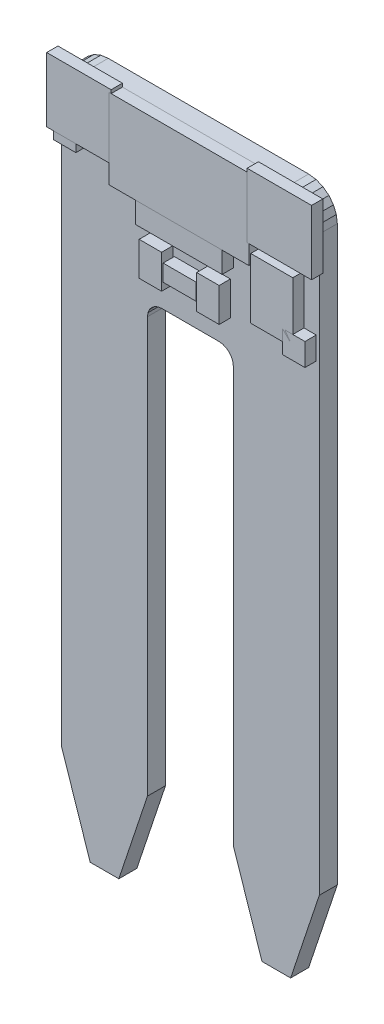
SolidWorks part; units mm, degrees
ref_plane "Front Plane" through (0, 0, 0) normal (0, 0, 1) x (1, 0, 0)
ref_plane "Top Plane" through (0, 0, 0) normal (0, 1, 0) x (1, 0, 0)
ref_plane "Right Plane" through (0, 0, 0) normal (1, 0, 0) x (0, 0, -1)
sketch "Sketch1" plane through (0, 0, 0) normal (0, 0, 1) x (1, 0, 0)
  line L0 (2.54, 60.96) -> (1.8826, 60.8735)
  line L1 (1.8826, 60.8735) -> (1.27, 60.6197)
  line L2 (1.27, 60.6197) -> (0.7439, 60.2161)
  line L3 (0.7439, 60.2161) -> (0.3403, 59.69)
  line L4 (0.3403, 59.69) -> (0.0865, 59.0774)
  line L5 (0.0865, 59.0774) -> (0, 58.42)
  line L6 (0, 58.42) -> (0, 7.62)
  line L7 (0, 7.62) -> (2.54, 0)
  line L8 (2.54, 0) -> (5.08, 0)
  line L9 (5.08, 0) -> (7.62, 7.62)
  line L10 (7.62, 7.62) -> (7.62, 44.45)
  line L11 (7.62, 44.45) -> (7.6633, 44.7787)
  line L12 (7.6633, 44.7787) -> (7.7901, 45.085)
  line L13 (7.7901, 45.085) -> (7.992, 45.348)
  line L14 (7.992, 45.348) -> (8.255, 45.5499)
  line L15 (8.255, 45.5499) -> (8.5613, 45.6767)
  line L16 (8.5613, 45.6767) -> (8.89, 45.72)
  line L17 (8.89, 45.72) -> (13.97, 45.72)
  line L18 (13.97, 45.72) -> (14.2987, 45.6767)
  line L19 (14.2987, 45.6767) -> (14.605, 45.5499)
  line L20 (14.605, 45.5499) -> (14.868, 45.348)
  line L21 (14.868, 45.348) -> (15.0699, 45.085)
  line L22 (15.0699, 45.085) -> (15.1967, 44.7787)
  line L23 (15.1967, 44.7787) -> (15.24, 44.45)
  line L24 (15.24, 44.45) -> (15.24, 7.62)
  line L25 (15.24, 7.62) -> (17.78, 0)
  line L26 (17.78, 0) -> (20.32, 0)
  line L27 (20.32, 0) -> (22.86, 7.62)
  line L28 (22.86, 7.62) -> (22.86, 58.42)
  line L29 (22.86, 58.42) -> (22.7735, 59.0774)
  line L30 (22.7735, 59.0774) -> (22.5197, 59.69)
  line L31 (22.5197, 59.69) -> (22.1161, 60.2161)
  line L32 (22.1161, 60.2161) -> (21.59, 60.6197)
  line L33 (21.59, 60.6197) -> (20.9774, 60.8735)
  line L34 (20.9774, 60.8735) -> (20.32, 60.96)
  line L35 (20.32, 60.96) -> (2.54, 60.96)
extrude "BOARD" add sketch "Sketch1" along normal blind 1.6 separate body
ref_plane "Plane1" through (0, 0, 1.6) normal (0, 0, 1) x (1, 0, 0)
sketch "Sketch2" plane through (0, 0, 1.6) normal (0, 0, 1) x (1, 0, 0)
  line L0 (2.27, 54.88) -> (0.27, 54.88)
  line L1 (0.27, 54.88) -> (0.27, 56.88)
  line L2 (0.27, 56.88) -> (2.27, 56.88)
  line L3 (2.27, 56.88) -> (2.27, 54.88)
extrude "FIDUCIAL-1X2-1" add sketch "Sketch2" along normal blind 1 separate body
sketch "Sketch3" plane through (0, 0, 1.6) normal (0, 0, 1) x (1, 0, 0)
  line L0 (22.59, 48.53) -> (20.59, 48.53)
  line L1 (20.59, 48.53) -> (20.59, 50.53)
  line L2 (20.59, 50.53) -> (22.59, 50.53)
  line L3 (22.59, 50.53) -> (22.59, 48.53)
extrude "FIDUCIAL-1X2-2" add sketch "Sketch3" along normal blind 1 separate body
sketch "Sketch5" plane through (0, 0, 1.6) normal (0, 0, 1) x (1, 0, 0)
  line L0 (7.5565, 57.7215) -> (15.24, 57.7215)
  line L1 (15.24, 57.7215) -> (15.24, 52.0065)
  line L2 (15.24, 52.0065) -> (7.5565, 52.0065)
  line L3 (7.5565, 52.0065) -> (7.5565, 57.7215)
extrude "MOLEX-1X3-1" add sketch "Sketch5" along normal blind 1 separate body
sketch "Sketch6" plane through (0, 0, 1.6) normal (0, 0, 1) x (1, 0, 0)
  line L0 (17.6098, 53.877) -> (5.2098, 53.877)
  line L1 (5.2098, 53.877) -> (5.2098, 60.9786)
  line L2 (5.2098, 60.9786) -> (17.6098, 60.9786)
  line L3 (17.6098, 60.9786) -> (17.6098, 53.877)
extrude "SCREWTERMINAL-3_5MM-3_LOCK_007S-1" add sketch "Sketch6" along normal blind 1 separate body
sketch "Sketch7" plane through (0, 0, 0) normal (0, 0, 1) x (1, 0, 0)
  line L0 (17.78, 53.45) -> (6.45, 53.45)
  line L1 (6.45, 53.45) -> (6.45, 48.26)
  line L2 (6.45, 48.26) -> (17.78, 48.26)
  line L3 (17.78, 48.26) -> (17.78, 53.45)
extrude "SFE_LOGO_NAME_FLAME__1-1" add sketch "Sketch7" against normal blind 1 separate body
sketch "Sketch8" plane through (0, 0, 0) normal (0, 0, 1) x (1, 0, 0)
  line L0 (21.8088, 56.0988) -> (18.8312, 56.0988)
  line L1 (18.8312, 56.0988) -> (18.8312, 53.428)
  line L2 (18.8312, 53.428) -> (21.8088, 53.428)
  line L3 (21.8088, 53.428) -> (21.8088, 56.0988)
extrude "OSHW-LOGO-S-1" add sketch "Sketch8" against normal blind 1 separate body
sketch "Sketch9" plane through (0, 0, 1.6) normal (0, 0, 1) x (1, 0, 0)
  line L0 (10.0076, 50.2666) -> (12.9286, 50.2666)
  line L1 (12.9286, 50.2666) -> (12.9286, 48.7934)
  line L2 (12.9286, 48.7934) -> (10.0076, 48.7934)
  line L3 (10.0076, 48.7934) -> (10.0076, 50.2666)
extrude "SOT23-3-1" add sketch "Sketch9" along normal blind 1 separate body
sketch "Sketch10" plane through (0, 0, 1.6) normal (0, 0, 1) x (1, 0, 0)
  line L0 (14.9784, 51.0284) -> (14.9784, 48.0316)
  line L1 (14.9784, 48.0316) -> (12.987, 48.0316)
  line L2 (12.987, 48.0316) -> (12.987, 51.0284)
  line L3 (12.987, 51.0284) -> (14.9784, 51.0284)
extrude "0603-RES-1" add sketch "Sketch10" along normal blind 1 separate body
sketch "Sketch11" plane through (0, 0, 1.6) normal (0, 0, 1) x (1, 0, 0)
  line L0 (7.8816, 48.0316) -> (7.8816, 51.0284)
  line L1 (7.8816, 51.0284) -> (9.873, 51.0284)
  line L2 (9.873, 51.0284) -> (9.873, 48.0316)
  line L3 (9.873, 48.0316) -> (7.8816, 48.0316)
extrude "0603-RES-2" add sketch "Sketch11" along normal blind 1 separate body
sketch "Sketch12" plane through (0, 0, 1.6) normal (0, 0, 1) x (1, 0, 0)
  line L0 (-0.3175, 61.2775) -> (5.3975, 61.2775)
  line L1 (5.3975, 61.2775) -> (5.3975, 55.5625)
  line L2 (5.3975, 55.5625) -> (-0.3175, 55.5625)
  line L3 (-0.3175, 55.5625) -> (-0.3175, 61.2775)
extrude "STAND-OFF-1" add sketch "Sketch12" along normal blind 1 separate body
sketch "Sketch13" plane through (0, 0, 1.6) normal (0, 0, 1) x (1, 0, 0)
  line L0 (17.4625, 61.2775) -> (23.1775, 61.2775)
  line L1 (23.1775, 61.2775) -> (23.1775, 55.5625)
  line L2 (23.1775, 55.5625) -> (17.4625, 55.5625)
  line L3 (17.4625, 55.5625) -> (17.4625, 61.2775)
extrude "STAND-OFF-2" add sketch "Sketch13" along normal blind 1 separate body
sketch "Sketch14" plane through (0, 0, 1.6) normal (0, 0, 1) x (1, 0, 0)
  line L0 (17.78, 54.89) -> (21.51, 54.89)
  line L1 (21.51, 54.89) -> (21.51, 49.53)
  line L2 (21.51, 49.53) -> (17.78, 49.53)
  line L3 (17.78, 49.53) -> (17.78, 54.89)
extrude "SFE_LOGO_FLAME__2-1" add sketch "Sketch14" along normal blind 1 separate body
